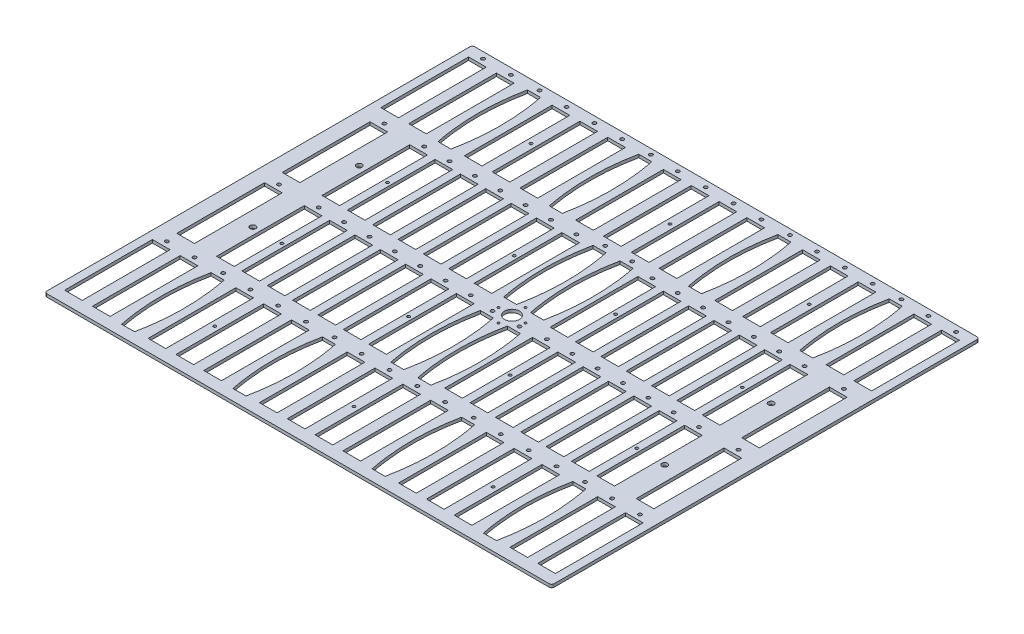
SolidWorks part; units mm, degrees
ref_plane "Front Plane" through (0, 0, 0) normal (0, 0, 1) x (1, 0, 0)
ref_plane "Top Plane" through (0, 0, 0) normal (0, 1, 0) x (1, 0, 0)
ref_plane "Right Plane" through (0, 0, 0) normal (1, 0, 0) x (0, 0, -1)
sketch "Sketch1" plane through (0, 0, 0) normal (0, 1, 0) x (1, 0, 0)
  line L1 (-262.7312, -221.6379) -> (262.7312, -221.6379)
  line L2 (-262.7312, -221.6379) -> (-262.7312, 221.6379)
  line L3 (-262.7312, 221.6379) -> (262.7312, 221.6379)
  line L4 (262.7312, -221.6379) -> (262.7312, 221.6379)
  line L5 (-262.7312, -221.6379) -> (262.7312, 221.6379) construction
  line L6 (-262.7312, 221.6379) -> (262.7312, -221.6379) construction
  point P0 (0, 0)
  dimension "D1" = 525.4625
  dimension "D2" = 443.2757
extrude "Boss-Extrude1" add sketch "Sketch1" along normal blind 3.175
sketch "Sketch2" plane through (0, 3.175, 0) normal (0, 1, 0) x (1, 0, 0)
  circle A0 centre (0, 0) radius 7.62
  dimension "D1" = 15.24
extrude "Cut-Extrude1" cut sketch "Sketch2" against normal through all
hole_wizard "#2 Clearance Hole1" positions "Sketch3" profile "Sketch4" hole size "#2" standard "ANSI Inch" end condition through all
sketch "Sketch3" plane through (0, 3.175, 0) normal (0, 1, 0) x (1, 0, 0)
  line L0 (0, 0) -> (0, 13.97) construction
  line L2 (0, 0) -> (13.97, 0) construction
  line L3 (0, 0) -> (0, -13.97) construction
  line L4 (0, 0) -> (-13.97, 0) construction
  point P194 (0, 13.97)
  point P202 (13.97, 0)
  point P203 (0, -13.97)
  point P204 (-13.97, 0)
  point P205 (0, 0)
  dimension "D1" = 4
  dimension "D2" = 13.97
sketch "Sketch4" plane through (0, 3.175, 0) normal (1, 0, 0) x (0, 0, 1)
  line L0 (0, 0) -> (0, 3.175)
  line L1 (0, 3.175) -> (1.2192, 3.175)
  line L2 (1.2192, 3.175) -> (1.2192, 0)
  line L5 (1.2192, 0) -> (0, 0)
  line L11 (0, -6.35) -> (0, 107.95) construction
  dimension "Thru Hole Dia." = 2.4384
  dimension "Thru Hole Depth" = 3.175
hole_wizard "#1 (0.228) Diameter Hole1" positions "Sketch6" profile "Sketch7" hole size "#1" standard "ANSI Inch" end condition through all
sketch "Sketch6" plane through (0, 3.175, 0) normal (0, 1, 0) x (1, 0, 0)
  line L1 (-213.36, -55.1011) -> (213.36, -55.1011) construction
  line L2 (-213.36, -55.1011) -> (-213.36, 55.1011) construction
  line L3 (-213.36, 55.1011) -> (213.36, 55.1011) construction
  line L4 (213.36, -55.1011) -> (213.36, 55.1011) construction
  line L5 (-213.36, -55.1011) -> (213.36, 55.1011) construction
  line L6 (-213.36, 55.1011) -> (213.36, -55.1011) construction
  circle A0 centre (0, 0) radius 7.62 construction
  point P2 (213.36, 55.1011)
  point P11 (-213.36, -55.1011)
  point P12 (-213.36, 55.1011)
  point P13 (213.36, -55.1011)
  point P26 (-213.36, 55.1011)
  point P28 (213.36, 55.1011)
  point P30 (213.36, -55.1011)
  point P32 (-213.36, -55.1011)
  dimension "D1" = 426.72
  dimension "D2" = 110.2021
  dimension "D3" = 213.36
  dimension "D4" = 55.1011
sketch "Sketch7" plane through (213.36, 3.175, -55.1011) normal (1, 0, 0) x (0, 0, 1)
  line L0 (0, 0) -> (0, 3.175)
  line L1 (0, 3.175) -> (2.8956, 3.175)
  line L2 (2.8956, 3.175) -> (2.8956, 0)
  line L5 (2.8956, 0) -> (0, 0)
  line L11 (0, -6.35) -> (0, 107.95) construction
  dimension "Thru Hole Dia." = 5.7912
  dimension "Thru Hole Depth" = 3.175
sketch "Sketch5" plane through (0, 3.175, 0) normal (0, 1, 0) x (1, 0, 0)
  line L0 (-262.7312, 163.8275) -> (262.7312, 163.8275) construction
  line L1 (-198.8875, 163.8275) -> (-176.0275, 163.8275) construction
  line L2 (-245.1367, 221.6379) -> (-245.1367, -221.6379) construction
  line L3 (-262.7312, 221.6379) -> (-262.7312, -221.6379) construction
  line L4 (-262.7312, -221.6379) -> (262.7312, -221.6379) construction
  line L5 (-216.2971, 221.6379) -> (-216.2971, -221.6379) construction
  line L6 (262.7312, -221.6379) -> (262.7312, 221.6379) construction
  line L7 (-187.4575, 221.6379) -> (-187.4575, -221.6379) construction
  line L8 (-262.7312, 54.6066) -> (262.7312, 54.6066) construction
  line L9 (-262.7312, -54.6142) -> (262.7312, -54.6142) construction
  line L10 (-262.7312, -163.8351) -> (262.7312, -163.8351) construction
  line L11 (262.7312, 221.6379) -> (-262.7312, 221.6379) construction
  line L12 (-158.6179, 221.6379) -> (-158.6179, -221.6379) construction
  line L13 (-129.7783, 221.6379) -> (-129.7783, -221.6379) construction
  line L14 (-100.9388, 221.6379) -> (-100.9388, -221.6379) construction
  line L15 (-72.0992, 221.6379) -> (-72.0992, -221.6379) construction
  line L16 (-43.2596, 221.6379) -> (-43.2596, -221.6379) construction
  line L17 (-14.42, 221.6379) -> (-14.42, -221.6379) construction
  line L18 (14.4196, 221.6379) -> (14.4196, -221.6379) construction
  line L19 (43.2592, 221.6379) -> (43.2592, -221.6379) construction
  line L20 (72.0987, 221.6379) -> (72.0987, -221.6379) construction
  line L21 (100.9383, 221.6379) -> (100.9383, -221.6379) construction
  line L22 (129.7779, 221.6379) -> (129.7779, -221.6379) construction
  line L23 (158.6175, 221.6379) -> (158.6175, -221.6379) construction
  line L24 (187.4571, 221.6379) -> (187.4571, -221.6379) construction
  line L25 (216.2967, 221.6379) -> (216.2967, -221.6379) construction
  line L26 (245.1362, 221.6379) -> (245.1362, -221.6379) construction
  line L27 (-225.4415, 209.2935) -> (-207.1535, 209.2935)
  line L28 (-254.2807, 209.2935) -> (-235.9927, 209.2935)
  line L29 (-254.2807, 209.2935) -> (-254.2807, 118.3615)
  line L30 (-254.2807, 118.3615) -> (-235.9927, 118.3615)
  line L31 (-235.9927, 209.2935) -> (-235.9927, 118.3615)
  line L32 (-254.2807, 209.2935) -> (-235.9927, 118.3615) construction
  line L33 (-254.2807, 118.3615) -> (-235.9927, 209.2935) construction
  line L34 (-254.2807, -118.3691) -> (-235.9927, -118.3691)
  line L35 (-254.2807, -118.3691) -> (-254.2807, -209.3011)
  line L36 (-254.2807, -209.3011) -> (-235.9927, -209.3011)
  line L37 (-235.9927, -118.3691) -> (-235.9927, -209.3011)
  line L38 (-254.2807, -118.3691) -> (-235.9927, -209.3011) construction
  line L39 (-254.2807, -209.3011) -> (-235.9927, -118.3691) construction
  line L40 (-225.4415, 209.2935) -> (-225.4415, 118.3615)
  line L41 (-207.1535, 209.2935) -> (-207.1535, 118.3615)
  line L42 (-225.4415, 118.3615) -> (-207.1535, 118.3615)
  line L43 (-225.4415, -118.3691) -> (-207.1535, -118.3691)
  line L44 (-207.1535, -118.3691) -> (-207.1535, -209.3011)
  line L45 (-225.4415, -118.3691) -> (-225.4415, -209.3011)
  line L46 (-225.4415, -209.3011) -> (-207.1535, -209.3011)
  line L47 (-194.1885, 210.1825) -> (-180.7265, 210.1825)
  line L48 (-194.1885, 210.1825) -> (-194.1885, 117.4725) construction
  line L49 (-194.1885, 117.4725) -> (-180.7265, 117.4725)
  line L50 (-180.7265, 210.1825) -> (-180.7265, 117.4725) construction
  line L51 (-194.1885, 210.1825) -> (-180.7265, 117.4725) construction
  line L52 (-194.1885, 117.4725) -> (-180.7265, 210.1825) construction
  line L53 (-78.8302, 210.1825) -> (-65.3682, 210.1825)
  line L54 (-78.8302, 117.4725) -> (-65.3682, 117.4725)
  line L55 (-167.7632, 209.2935) -> (-149.4752, 209.2935)
  line L56 (-167.7632, 209.2935) -> (-167.7632, 118.3615)
  line L57 (-149.4752, 209.2935) -> (-149.4752, 118.3615)
  line L58 (-167.7632, 118.3615) -> (-149.4752, 118.3615)
  line L59 (-167.7632, -118.3691) -> (-149.4752, -118.3691)
  line L60 (-149.4752, -118.3691) -> (-149.4752, -209.3011)
  line L61 (-167.7632, -118.3691) -> (-167.7632, -209.3011)
  line L62 (-167.7632, -209.3011) -> (-149.4752, -209.3011)
  line L63 (-138.924, 209.2935) -> (-120.636, 209.2935)
  line L64 (-138.924, 209.2935) -> (-138.924, 118.3615)
  line L65 (-120.636, 209.2935) -> (-120.636, 118.3615)
  line L66 (-138.924, 118.3615) -> (-120.636, 118.3615)
  line L67 (-138.924, -118.3691) -> (-120.636, -118.3691)
  line L68 (-120.636, -118.3691) -> (-120.636, -209.3011)
  line L69 (-138.924, -118.3691) -> (-138.924, -209.3011)
  line L70 (-138.924, -209.3011) -> (-120.636, -209.3011)
  line L71 (-110.0849, 209.2935) -> (-91.7969, 209.2935)
  line L72 (-110.0849, 209.2935) -> (-110.0849, 118.3615)
  line L73 (-91.7969, 209.2935) -> (-91.7969, 118.3615)
  line L74 (-110.0849, 118.3615) -> (-91.7969, 118.3615)
  line L75 (-110.0849, -118.3691) -> (-91.7969, -118.3691)
  line L76 (-91.7969, -118.3691) -> (-91.7969, -209.3011)
  line L77 (-110.0849, -118.3691) -> (-110.0849, -209.3011)
  line L78 (-110.0849, -209.3011) -> (-91.7969, -209.3011)
  line L79 (65.3677, 210.1825) -> (78.8297, 210.1825)
  line L80 (65.3677, 117.4725) -> (78.8297, 117.4725)
  line L81 (180.7261, 210.1825) -> (194.1881, 210.1825)
  line L82 (180.7261, 117.4725) -> (194.1881, 117.4725)
  line L83 (-194.1885, -117.6299) -> (-180.7265, -117.6299)
  line L84 (-194.1885, -210.3399) -> (-180.7265, -210.3399)
  line L85 (-78.8302, -117.6299) -> (-65.3682, -117.6299)
  line L86 (-78.8302, -210.3399) -> (-65.3682, -210.3399)
  line L87 (-52.4065, 209.2935) -> (-34.1185, 209.2935)
  line L88 (-52.4065, 209.2935) -> (-52.4065, 118.3615)
  line L89 (-34.1185, 209.2935) -> (-34.1185, 118.3615)
  line L90 (-52.4065, 118.3615) -> (-34.1185, 118.3615)
  line L91 (-52.4065, -118.3691) -> (-34.1185, -118.3691)
  line L92 (-34.1185, -118.3691) -> (-34.1185, -209.3011)
  line L93 (-52.4065, -118.3691) -> (-52.4065, -209.3011)
  line L94 (-52.4065, -209.3011) -> (-34.1185, -209.3011)
  line L95 (-23.5674, 209.2935) -> (-5.2794, 209.2935)
  line L96 (-23.5674, 209.2935) -> (-23.5674, 118.3615)
  line L97 (-5.2794, 209.2935) -> (-5.2794, 118.3615)
  line L98 (-23.5674, 118.3615) -> (-5.2794, 118.3615)
  line L99 (-23.5674, -118.3691) -> (-5.2794, -118.3691)
  line L100 (-5.2794, -118.3691) -> (-5.2794, -209.3011)
  line L101 (-23.5674, -118.3691) -> (-23.5674, -209.3011)
  line L102 (-23.5674, -209.3011) -> (-5.2794, -209.3011)
  line L103 (5.2718, 209.2935) -> (23.5598, 209.2935)
  line L104 (5.2718, 209.2935) -> (5.2718, 118.3615)
  line L105 (23.5598, 209.2935) -> (23.5598, 118.3615)
  line L106 (5.2718, 118.3615) -> (23.5598, 118.3615)
  line L107 (5.2718, -118.3691) -> (23.5598, -118.3691)
  line L108 (23.5598, -118.3691) -> (23.5598, -209.3011)
  line L109 (5.2718, -118.3691) -> (5.2718, -209.3011)
  line L110 (5.2718, -209.3011) -> (23.5598, -209.3011)
  line L111 (34.1109, 209.2935) -> (52.3989, 209.2935)
  line L112 (34.1109, 209.2935) -> (34.1109, 118.3615)
  line L113 (52.3989, 209.2935) -> (52.3989, 118.3615)
  line L114 (34.1109, 118.3615) -> (52.3989, 118.3615)
  line L115 (34.1109, -118.3691) -> (52.3989, -118.3691)
  line L116 (52.3989, -118.3691) -> (52.3989, -209.3011)
  line L117 (34.1109, -118.3691) -> (34.1109, -209.3011)
  line L118 (34.1109, -209.3011) -> (52.3989, -209.3011)
  line L119 (180.7261, -117.6299) -> (194.1881, -117.6299)
  line L120 (180.7261, -210.3399) -> (194.1881, -210.3399)
  line L121 (65.3677, -210.3399) -> (78.8297, -210.3399)
  line L122 (65.3677, -117.6299) -> (78.8297, -117.6299)
  line L127 (91.7892, 209.2935) -> (110.0772, 209.2935)
  line L128 (91.7892, 209.2935) -> (91.7893, 118.3615)
  line L129 (110.0772, 209.2935) -> (110.0773, 118.3615)
  line L130 (91.7893, 118.3615) -> (110.0773, 118.3615)
  line L131 (91.7893, -118.3691) -> (110.0773, -118.3691)
  line L132 (110.0773, -118.3691) -> (110.0773, -209.3011)
  line L133 (91.7893, -118.3691) -> (91.7893, -209.3011)
  line L134 (91.7893, -209.3011) -> (110.0773, -209.3011)
  line L135 (120.6284, 209.2935) -> (138.9164, 209.2935)
  line L136 (120.6284, 209.2935) -> (120.6284, 118.3615)
  line L137 (138.9164, 209.2935) -> (138.9164, 118.3615)
  line L138 (120.6284, 118.3615) -> (138.9164, 118.3615)
  line L139 (120.6284, -118.3691) -> (138.9164, -118.3691)
  line L140 (138.9164, -118.3691) -> (138.9164, -209.3011)
  line L141 (120.6284, -118.3691) -> (120.6284, -209.3011)
  line L142 (120.6284, -209.3011) -> (138.9164, -209.3011)
  line L143 (149.4676, 209.2935) -> (167.7556, 209.2935)
  line L144 (149.4676, 209.2935) -> (149.4676, 118.3615)
  line L145 (167.7556, 209.2935) -> (167.7556, 118.3615)
  line L146 (149.4676, 118.3615) -> (167.7556, 118.3615)
  line L147 (149.4676, -118.3691) -> (167.7556, -118.3691)
  line L148 (167.7556, -118.3691) -> (167.7556, -209.3011)
  line L149 (149.4676, -118.3691) -> (149.4676, -209.3011)
  line L150 (149.4676, -209.3011) -> (167.7556, -209.3011)
  line L159 (207.1459, 209.2935) -> (225.4339, 209.2935)
  line L160 (207.1459, 209.2935) -> (207.1459, 118.3615)
  line L161 (225.4339, 209.2935) -> (225.4339, 118.3615)
  line L162 (207.1459, 118.3615) -> (225.4339, 118.3615)
  line L163 (207.1459, -118.3691) -> (225.4339, -118.3691)
  line L164 (225.4339, -118.3691) -> (225.4339, -209.3011)
  line L165 (207.1459, -118.3691) -> (207.1459, -209.3011)
  line L166 (207.1459, -209.3011) -> (225.4339, -209.3011)
  line L167 (235.985, 209.2935) -> (254.2731, 209.2935)
  line L168 (235.985, 209.2935) -> (235.9851, 118.3615)
  line L169 (254.2731, 209.2935) -> (254.2731, 118.3615)
  line L170 (235.9851, 118.3615) -> (254.2731, 118.3615)
  line L171 (235.9851, -118.3691) -> (254.2731, -118.3691)
  line L172 (254.2731, -118.3691) -> (254.2731, -209.3011)
  line L173 (235.9851, -118.3691) -> (235.9851, -209.3011)
  line L174 (235.9851, -209.3011) -> (254.2731, -209.3011)
  line L337 (-178.3143, 209.2935) -> (-178.3143, 118.3615) [skipped]
  line L338 (-196.6023, 118.3615) -> (-178.3143, 118.3615) [skipped]
  line L339 (-196.6023, 209.2935) -> (-196.6023, 118.3615) [skipped]
  line L340 (-196.6023, 209.2935) -> (-178.3143, 209.2935) [skipped]
  line L341 (-62.9577, 209.2935) -> (-62.9577, 118.3615) [skipped]
  line L342 (-81.2457, 209.2935) -> (-62.9577, 209.2935) [skipped]
  line L343 (-81.2457, 209.2935) -> (-81.2457, 118.3615) [skipped]
  line L344 (-81.2457, 118.3615) -> (-62.9577, 118.3615) [skipped]
  line L345 (-196.6023, -118.3691) -> (-178.3143, -118.3691) [skipped]
  line L346 (-196.6023, -209.3011) -> (-178.3143, -209.3011) [skipped]
  line L347 (-178.3143, -118.3691) -> (-178.3143, -209.3011) [skipped]
  line L348 (-196.6023, -118.3691) -> (-196.6023, -209.3011) [skipped]
  line L349 (-81.2457, -118.3691) -> (-62.9577, -118.3691) [skipped]
  line L350 (-81.2457, -118.3691) -> (-81.2457, -209.3011) [skipped]
  line L351 (-62.9577, -118.3691) -> (-62.9577, -209.3011) [skipped]
  line L352 (-81.2457, -209.3011) -> (-62.9577, -209.3011) [skipped]
  line L353 (178.3067, -118.3691) -> (196.5947, -118.3691) [skipped]
  line L354 (196.5947, -118.3691) -> (196.5947, -209.3011) [skipped]
  line L355 (178.3067, -118.3691) -> (178.3067, -209.3011) [skipped]
  line L356 (178.3067, -209.3011) -> (196.5947, -209.3011) [skipped]
  line L357 (62.9501, -209.3011) -> (81.2381, -209.3011) [skipped]
  line L358 (81.2381, -118.3691) -> (81.2381, -209.3011) [skipped]
  line L359 (62.9501, -118.3691) -> (62.9501, -209.3011) [skipped]
  line L360 (62.9501, -118.3691) -> (81.2381, -118.3691) [skipped]
  line L361 (178.3067, 118.3615) -> (196.5947, 118.3615) [skipped]
  line L362 (196.5947, 209.2935) -> (196.5947, 118.3615) [skipped]
  line L363 (178.3067, 209.2935) -> (178.3067, 118.3615) [skipped]
  line L364 (178.3067, 209.2935) -> (196.5947, 209.2935) [skipped]
  line L365 (62.9501, 118.3615) -> (81.2381, 118.3615) [skipped]
  line L366 (62.9501, 209.2935) -> (62.9501, 118.3615) [skipped]
  line L367 (81.2381, 209.2935) -> (81.2381, 118.3615) [skipped]
  line L368 (62.9501, 209.2935) -> (81.2381, 209.2935) [skipped]
  circle A0 centre (-245.1367, 215.1355) radius 1.8288
  circle A1 centre (-245.1367, -112.5271) radius 1.8288
  circle A2 centre (-216.2975, 215.1355) radius 1.8288
  circle A3 centre (-216.2975, -112.5271) radius 1.8288
  circle A4 centre (-187.4575, 216.0245) radius 1.8288
  circle A5 centre (-72.0992, 216.0245) radius 1.8288
  circle A6 centre (-158.6192, 215.1355) radius 1.8288
  circle A7 centre (-158.6192, -112.5271) radius 1.8288
  circle A8 centre (-129.78, 215.1355) radius 1.8288
  circle A9 centre (-129.78, -112.5271) radius 1.8288
  circle A10 centre (-100.9409, 215.1355) radius 1.8288
  circle A11 centre (-100.9409, -112.5271) radius 1.8288
  circle A12 centre (72.0987, 216.0245) radius 1.8288
  circle A13 centre (187.4571, 216.0245) radius 1.8288
  circle A14 centre (-43.2625, 215.1355) radius 1.8288
  circle A15 centre (-43.2625, -112.5271) radius 1.8288
  circle A16 centre (-14.4234, 215.1355) radius 1.8288
  circle A17 centre (-14.4234, -112.5271) radius 1.8288
  circle A18 centre (14.4158, 215.1355) radius 1.8288
  circle A19 centre (14.4158, -112.5271) radius 1.8288
  circle A20 centre (43.2549, 215.1355) radius 1.8288
  circle A21 centre (43.2549, -112.5271) radius 1.8288
  circle A22 centre (-187.4575, -111.7879) radius 1.8288
  circle A23 centre (-72.0992, -111.7879) radius 1.8288
  circle A24 centre (100.9333, 215.1355) radius 1.8288
  circle A25 centre (100.9333, -112.5271) radius 1.8288
  circle A26 centre (129.7724, 215.1355) radius 1.8288
  circle A27 centre (129.7724, -112.5271) radius 1.8288
  circle A28 centre (158.6116, 215.1355) radius 1.8288
  circle A29 centre (158.6116, -112.5271) radius 1.8288
  circle A30 centre (187.4571, -111.7879) radius 1.8288
  circle A31 centre (72.0987, -111.7879) radius 1.8288
  circle A32 centre (216.2899, 215.1355) radius 1.8288
  circle A33 centre (216.2899, -112.5271) radius 1.8288
  circle A34 centre (245.129, 215.1355) radius 1.8288
  circle A35 centre (245.1291, -112.5271) radius 1.8288
  circle A36 centre (-72.1017, 215.1355) radius 1.8288 [skipped]
  circle A37 centre (-187.4583, 215.1355) radius 1.8288 [skipped]
  circle A38 centre (-187.4583, -112.5271) radius 1.8288 [skipped]
  circle A39 centre (-72.1017, -112.5271) radius 1.8288 [skipped]
  circle A40 centre (187.4507, -112.5271) radius 1.8288 [skipped]
  circle A41 centre (72.0941, -112.5271) radius 1.8288 [skipped]
  circle A42 centre (187.4507, 215.1355) radius 1.8288 [skipped]
  circle A43 centre (72.0941, 215.1355) radius 1.8288 [skipped]
  spline S0 degree 2 poles (-180.7265, 210.1825) (-171.3285, 163.8275) (-180.7265, 117.4725) knots 0 0 0 1 1 1
  spline S1 degree 2 poles (-194.1885, 210.1825) (-203.5865, 163.8275) (-194.1885, 117.4725) knots 0 0 0 1 1 1
  spline S2 degree 2 poles (-78.8302, 210.1825) (-88.2282, 163.8275) (-78.8302, 117.4725) knots 0 0 0 1 1 1
  spline S3 degree 2 poles (-65.3682, 210.1825) (-55.9702, 163.8275) (-65.3682, 117.4725) knots 0 0 0 1 1 1
  spline S4 degree 2 poles (65.3677, 210.1825) (55.9697, 163.8275) (65.3677, 117.4725) knots 0 0 0 1 1 1
  spline S5 degree 2 poles (78.8297, 210.1825) (88.2277, 163.8275) (78.8297, 117.4725) knots 0 0 0 1 1 1
  spline S6 degree 2 poles (194.1881, 210.1825) (203.5861, 163.8275) (194.1881, 117.4725) knots 0 0 0 1 1 1
  spline S7 degree 2 poles (180.7261, 210.1825) (171.3281, 163.8275) (180.7261, 117.4725) knots 0 0 0 1 1 1
  spline S8 degree 2 poles (-194.1885, -117.6299) (-203.5865, -163.9849) (-194.1885, -210.3399) knots 0 0 0 1 1 1
  spline S9 degree 2 poles (-180.7265, -117.6299) (-171.3285, -163.9849) (-180.7265, -210.3399) knots 0 0 0 1 1 1
  spline S10 degree 2 poles (-65.3682, -117.6299) (-55.9702, -163.9849) (-65.3682, -210.3399) knots 0 0 0 1 1 1
  spline S11 degree 2 poles (-78.8302, -117.6299) (-88.2282, -163.9849) (-78.8302, -210.3399) knots 0 0 0 1 1 1
  spline S12 degree 2 poles (194.1881, -117.6299) (203.5861, -163.9849) (194.1881, -210.3399) knots 0 0 0 1 1 1
  spline S13 degree 2 poles (180.7261, -117.6299) (171.3281, -163.9849) (180.7261, -210.3399) knots 0 0 0 1 1 1
  spline S14 degree 2 poles (78.8297, -117.6299) (88.2277, -163.9849) (78.8297, -210.3399) knots 0 0 0 1 1 1
  spline S15 degree 2 poles (65.3677, -117.6299) (55.9697, -163.9849) (65.3677, -210.3399) knots 0 0 0 1 1 1
  point P18 (-245.1367, 163.8275)
  point P57 (-245.1367, -163.8351)
  point P66 (-187.4575, 163.8275)
  point P86 (-187.4575, 163.8275)
  dimension "D6" = 3.6576
  dimension "D7" = 5.842
  dimension "D8" = 5.842
  dimension "D13" = 5.842
  dimension "D1" = 4
  dimension "D3" = 17.5946
  dimension "D5" = 90.932
  dimension "D2" = 57.8104
  dimension "D4" = 18.288
  dimension "D10" = 13.462
  dimension "D11" = 92.71
  dimension "D12" = 22.86
  dimension "D9" = 18
  dimension "D14" = 2
  dimension "D15" = 2
extrude "Cut-Extrude3" cut sketch "Sketch5" against normal blind 3.175
hole_wizard "#6 Clearance Hole2" positions "Sketch9" profile "Sketch10" hole size "#6" standard "ANSI Inch" end condition through all
sketch "Sketch9" plane through (0, 3.175, 0) normal (0, 1, 0) x (1, 0, 0)
  line L0 (-245.1367, 209.2935) -> (-245.1367, 215.1355) construction
  line L1 (-235.9927, 209.2935) -> (-254.2807, 209.2935) construction
  point P2 (-245.1367, 215.1355)
  dimension "D1" = 5.842
sketch "Sketch10" plane through (-245.1367, 3.175, -215.1355) normal (1, 0, 0) x (0, 0, 1)
  line L0 (0, 0) -> (0, 3.175)
  line L1 (0, 3.175) -> (1.8288, 3.175)
  line L2 (1.8288, 3.175) -> (1.8288, 0)
  line L5 (1.8288, 0) -> (0, 0)
  line L11 (0, -6.35) -> (0, 107.95) construction
  dimension "Thru Hole Dia." = 3.6576
  dimension "Thru Hole Depth" = 3.175
sketch "Sketch11" plane through (0, 3.175, 0) normal (0, 1, 0) x (1, 0, 0)
  line L0 (-262.7312, 163.8275) -> (262.7312, 163.8275) construction
  line L1 (-262.7312, 221.6379) -> (-262.7312, -221.6379) construction
  line L2 (262.7312, -221.6379) -> (262.7312, 221.6379) construction
  line L3 (262.7312, 221.6379) -> (-262.7312, 221.6379) construction
  line L4 (-262.7312, 54.5567) -> (262.7312, 54.5567) construction
  line L5 (-262.7312, -54.7141) -> (262.7312, -54.7141) construction
  line L6 (-262.7312, -163.9849) -> (262.7312, -163.9849) construction
  line L7 (-238.045, 100.0227) -> (-238.045, 105.8647) construction
  line L8 (-247.189, 100.0227) -> (-228.901, 100.0227)
  line L9 (-247.189, 100.0227) -> (-247.189, 9.0907)
  line L10 (-247.189, 9.0907) -> (-228.901, 9.0907)
  line L11 (-228.901, 100.0227) -> (-228.901, 9.0907)
  line L12 (-247.189, 100.0227) -> (-228.901, 9.0907) construction
  line L13 (-247.189, 9.0907) -> (-228.901, 100.0227) construction
  line L14 (228.901, 100.0227) -> (247.189, 100.0227)
  line L15 (228.901, 100.0227) -> (228.901, 9.0907)
  line L16 (247.189, 100.0227) -> (247.189, 9.0907)
  line L17 (228.901, 9.0907) -> (247.189, 9.0907)
  line L18 (228.901, -9.2481) -> (247.189, -9.2481)
  line L19 (228.901, -9.2481) -> (228.901, -100.1801)
  line L20 (247.189, -9.2481) -> (247.189, -100.1801)
  line L21 (228.901, -100.1801) -> (247.189, -100.1801)
  line L22 (-247.189, -9.2481) -> (-228.901, -9.2481)
  line L23 (-247.189, -9.2481) -> (-247.189, -100.1801)
  line L24 (-228.901, -9.2481) -> (-228.901, -100.1801)
  line L25 (-247.189, -100.1801) -> (-228.901, -100.1801)
  circle A0 centre (-238.045, 105.8647) radius 1.8288
  circle A1 centre (238.045, 105.8647) radius 1.8288
  circle A2 centre (238.045, -3.4061) radius 1.8288
  circle A3 centre (-238.045, -3.4061) radius 1.8288
  point P8 (-238.045, 54.5567)
  dimension "D5" = 3.6576
  dimension "D1" = 57.8104
  dimension "D2" = 24.6863
  dimension "D3" = 18.288
  dimension "D4" = 90.932
  dimension "D6" = 5.842
extrude "Cut-Extrude5" cut sketch "Sketch11" against normal blind 3.175
sketch "Sketch12" plane through (0, 3.175, 0) normal (0, 1, 0) x (1, 0, 0)
  line L0 (-228.901, 54.5567) -> (228.901, 54.5567) construction
  line L1 (-228.901, 9.0907) -> (-228.901, 100.0227) construction
  line L2 (228.901, 100.0227) -> (228.901, 9.0907) construction
  line L3 (-213.36, 55.1011) -> (-213.36, 247.1712) construction
  line L4 (-247.189, 9.0907) -> (-228.901, 9.0907) construction
  line L5 (-205.994, 100.0227) -> (-187.706, 100.0227)
  line L6 (-205.994, 100.0227) -> (-205.994, 9.0907)
  line L7 (-205.994, 9.0907) -> (-187.706, 9.0907)
  line L8 (-187.706, 100.0227) -> (-187.706, 9.0907)
  line L9 (-205.994, 100.0227) -> (-187.706, 9.0907) construction
  line L10 (-205.994, 9.0907) -> (-187.706, 100.0227) construction
  line L11 (-196.85, 100.0227) -> (-196.85, 105.8647) construction
  line L12 (-179.7209, 100.0227) -> (-161.4329, 100.0227)
  line L13 (-179.7209, 100.0227) -> (-179.7209, 9.0907)
  line L14 (-161.4329, 100.0227) -> (-161.4329, 9.0907)
  line L15 (-179.7209, 9.0907) -> (-161.4329, 9.0907)
  line L16 (-153.4477, 100.0227) -> (-135.1597, 100.0227)
  line L17 (-153.4477, 100.0227) -> (-153.4477, 9.0907)
  line L18 (-135.1597, 100.0227) -> (-135.1597, 9.0907)
  line L19 (-153.4477, 9.0907) -> (-135.1597, 9.0907)
  line L20 (-127.1746, 100.0227) -> (-108.8866, 100.0227)
  line L21 (-127.1746, 100.0227) -> (-127.1746, 9.0907)
  line L22 (-108.8866, 100.0227) -> (-108.8866, 9.0907)
  line L23 (-127.1746, 9.0907) -> (-108.8866, 9.0907)
  line L24 (-100.9015, 100.0227) -> (-82.6135, 100.0227)
  line L25 (-100.9015, 100.0227) -> (-100.9015, 9.0907)
  line L26 (-82.6135, 100.0227) -> (-82.6135, 9.0907)
  line L27 (-100.9015, 9.0907) -> (-82.6135, 9.0907)
  line L28 (-74.6284, 100.0227) -> (-56.3404, 100.0227)
  line L29 (-74.6284, 100.0227) -> (-74.6284, 9.0907)
  line L30 (-56.3404, 100.0227) -> (-56.3404, 9.0907)
  line L31 (-74.6284, 9.0907) -> (-56.3404, 9.0907)
  line L32 (-48.3552, 100.0227) -> (-30.0672, 100.0227)
  line L33 (-48.3552, 100.0227) -> (-48.3552, 9.0907)
  line L34 (-30.0672, 100.0227) -> (-30.0672, 9.0907)
  line L35 (-48.3552, 9.0907) -> (-30.0672, 9.0907)
  line L36 (0, 0) -> (0, 123.4666) construction
  line L37 (-13.97, 58.3667) -> (13.97, 58.3667) construction
  line L38 (-2.54, 58.3667) -> (-25.4, 58.3667) construction
  line L39 (-7.239, 104.7217) -> (-20.701, 104.7217)
  line L40 (-7.239, 104.7217) -> (-7.239, 12.0117) construction
  line L41 (-7.239, 12.0117) -> (-20.701, 12.0117)
  line L42 (-20.701, 104.7217) -> (-20.701, 12.0117) construction
  line L43 (-7.239, 104.7217) -> (-20.701, 12.0117) construction
  line L44 (30.4641, 100.0227) -> (48.7521, 100.0227)
  line L45 (30.4641, 100.0227) -> (30.4641, 9.0907)
  line L46 (48.7521, 100.0227) -> (48.7521, 9.0907)
  line L47 (30.4641, 9.0907) -> (48.7521, 9.0907)
  line L48 (56.7373, 100.0227) -> (75.0253, 100.0227)
  line L49 (56.7373, 100.0227) -> (56.7373, 9.0907)
  line L50 (75.0253, 100.0227) -> (75.0253, 9.0907)
  line L51 (56.7373, 9.0907) -> (75.0253, 9.0907)
  line L52 (83.0104, 100.0227) -> (101.2984, 100.0227)
  line L53 (83.0104, 100.0227) -> (83.0104, 9.0907)
  line L54 (101.2984, 100.0227) -> (101.2984, 9.0907)
  line L55 (83.0104, 9.0907) -> (101.2984, 9.0907)
  line L56 (109.2835, 100.0227) -> (127.5715, 100.0227)
  line L57 (109.2835, 100.0227) -> (109.2835, 9.0907)
  line L58 (127.5715, 100.0227) -> (127.5715, 9.0907)
  line L59 (109.2835, 9.0907) -> (127.5715, 9.0907)
  line L60 (135.5566, 100.0227) -> (153.8446, 100.0227)
  line L61 (135.5566, 100.0227) -> (135.5566, 9.0907)
  line L62 (153.8446, 100.0227) -> (153.8446, 9.0907)
  line L63 (135.5566, 9.0907) -> (153.8446, 9.0907)
  line L64 (161.8298, 100.0227) -> (180.1178, 100.0227)
  line L65 (161.8298, 100.0227) -> (161.8298, 9.0907)
  line L66 (180.1178, 100.0227) -> (180.1178, 9.0907)
  line L67 (161.8298, 9.0907) -> (180.1178, 9.0907)
  line L68 (188.1029, 100.0227) -> (206.3909, 100.0227)
  line L69 (188.1029, 100.0227) -> (188.1029, 9.0907)
  line L70 (206.3909, 100.0227) -> (206.3909, 9.0907)
  line L71 (188.1029, 9.0907) -> (206.3909, 9.0907)
  line L72 (-179.7209, -9.2481) -> (-161.4329, -9.2481)
  line L73 (-179.7209, -9.2481) -> (-179.7209, -100.1801)
  line L74 (-161.4329, -9.2481) -> (-161.4329, -100.1801)
  line L75 (-179.7209, -100.1801) -> (-161.4329, -100.1801)
  line L76 (-153.4477, -9.2481) -> (-135.1597, -9.2481)
  line L77 (-153.4477, -9.2481) -> (-153.4477, -100.1801)
  line L78 (-135.1597, -9.2481) -> (-135.1597, -100.1801)
  line L79 (-153.4477, -100.1801) -> (-135.1597, -100.1801)
  line L80 (-127.1746, -9.2481) -> (-108.8866, -9.2481)
  line L81 (-127.1746, -9.2481) -> (-127.1746, -100.1801)
  line L82 (-108.8866, -9.2481) -> (-108.8866, -100.1801)
  line L83 (-127.1746, -100.1801) -> (-108.8866, -100.1801)
  line L84 (-100.9015, -9.2481) -> (-82.6135, -9.2481)
  line L85 (-100.9015, -9.2481) -> (-100.9015, -100.1801)
  line L86 (-82.6135, -9.2481) -> (-82.6135, -100.1801)
  line L87 (-100.9015, -100.1801) -> (-82.6135, -100.1801)
  line L88 (-74.6284, -9.2481) -> (-56.3404, -9.2481)
  line L89 (-74.6284, -9.2481) -> (-74.6284, -100.1801)
  line L90 (-56.3404, -9.2481) -> (-56.3404, -100.1801)
  line L91 (-74.6284, -100.1801) -> (-56.3404, -100.1801)
  line L92 (-48.3552, -9.2481) -> (-30.0672, -9.2481)
  line L93 (-48.3552, -9.2481) -> (-48.3552, -100.1801)
  line L94 (-30.0672, -9.2481) -> (-30.0672, -100.1801)
  line L95 (-48.3552, -100.1801) -> (-30.0672, -100.1801)
  line L96 (-7.239, 12.0117) -> (-20.701, 104.7217) construction
  line L97 (-13.97, 104.7217) -> (-13.97, 110.5637) construction
  line L98 (2.54, 58.3667) -> (25.4, 58.3667) construction
  line L99 (7.239, 12.0117) -> (20.701, 12.0117)
  line L100 (7.239, 12.0117) -> (7.239, 104.7217) construction
  line L101 (7.239, 104.7217) -> (20.701, 104.7217)
  line L102 (20.701, 12.0117) -> (20.701, 104.7217) construction
  line L103 (7.239, 12.0117) -> (20.701, 104.7217) construction
  line L104 (30.4641, -9.2481) -> (48.7521, -9.2481)
  line L105 (30.4641, -9.2481) -> (30.4641, -100.1801)
  line L106 (48.7521, -9.2481) -> (48.7521, -100.1801)
  line L107 (30.4641, -100.1801) -> (48.7521, -100.1801)
  line L108 (56.7373, -9.2481) -> (75.0253, -9.2481)
  line L109 (56.7373, -9.2481) -> (56.7373, -100.1801)
  line L110 (75.0253, -9.2481) -> (75.0253, -100.1801)
  line L111 (56.7373, -100.1801) -> (75.0253, -100.1801)
  line L112 (83.0104, -9.2481) -> (101.2984, -9.2481)
  line L113 (83.0104, -9.2481) -> (83.0104, -100.1801)
  line L114 (101.2984, -9.2481) -> (101.2984, -100.1801)
  line L115 (83.0104, -100.1801) -> (101.2984, -100.1801)
  line L116 (109.2835, -9.2481) -> (127.5715, -9.2481)
  line L117 (109.2835, -9.2481) -> (109.2835, -100.1801)
  line L118 (127.5715, -9.2481) -> (127.5715, -100.1801)
  line L119 (109.2835, -100.1801) -> (127.5715, -100.1801)
  line L120 (135.5566, -9.2481) -> (153.8446, -9.2481)
  line L121 (135.5566, -9.2481) -> (135.5566, -100.1801)
  line L122 (153.8446, -9.2481) -> (153.8446, -100.1801)
  line L123 (135.5566, -100.1801) -> (153.8446, -100.1801)
  line L124 (161.8298, -9.2481) -> (180.1178, -9.2481)
  line L125 (161.8298, -9.2481) -> (161.8298, -100.1801)
  line L126 (180.1178, -9.2481) -> (180.1178, -100.1801)
  line L127 (161.8298, -100.1801) -> (180.1178, -100.1801)
  line L128 (188.1029, -9.2481) -> (206.3909, -9.2481)
  line L129 (188.1029, -9.2481) -> (188.1029, -100.1801)
  line L130 (206.3909, -9.2481) -> (206.3909, -100.1801)
  line L131 (188.1029, -100.1801) -> (206.3909, -100.1801)
  line L132 (-205.994, -9.2481) -> (-187.706, -9.2481)
  line L133 (-205.994, -9.2481) -> (-205.994, -100.1801)
  line L134 (-187.706, -9.2481) -> (-187.706, -100.1801)
  line L135 (-205.994, -100.1801) -> (-187.706, -100.1801)
  line L136 (-22.0821, 100.0227) -> (-3.7941, 100.0227) [skipped]
  line L137 (-22.0821, 100.0227) -> (-22.0821, 9.0907) [skipped]
  line L138 (-3.7941, 100.0227) -> (-3.7941, 9.0907) [skipped]
  line L139 (-22.0821, 9.0907) -> (-3.7941, 9.0907) [skipped]
  line L140 (4.191, 100.0227) -> (22.479, 100.0227) [skipped]
  line L141 (4.191, 100.0227) -> (4.191, 9.0907) [skipped]
  line L142 (22.479, 100.0227) -> (22.479, 9.0907) [skipped]
  line L143 (4.191, 9.0907) -> (22.479, 9.0907) [skipped]
  line L144 (-22.0821, -9.2481) -> (-3.7941, -9.2481) [skipped]
  line L145 (-22.0821, -9.2481) -> (-22.0821, -100.1801) [skipped]
  line L146 (-3.7941, -9.2481) -> (-3.7941, -100.1801) [skipped]
  line L147 (-22.0821, -100.1801) -> (-3.7941, -100.1801) [skipped]
  line L148 (4.191, -9.2481) -> (22.479, -9.2481) [skipped]
  line L149 (4.191, -9.2481) -> (4.191, -100.1801) [skipped]
  line L150 (22.479, -9.2481) -> (22.479, -100.1801) [skipped]
  line L151 (4.191, -100.1801) -> (22.479, -100.1801) [skipped]
  line L152 (7.239, 104.7217) -> (20.701, 12.0117) construction
  line L154 (13.97, 104.7217) -> (13.97, 110.5637) construction
  line L155 (-7.239, -12.1183) -> (-20.701, -12.1183)
  line L156 (7.239, -12.1183) -> (20.701, -12.1183)
  line L157 (7.239, -104.8283) -> (20.701, -104.8283)
  line L158 (-7.239, -104.8283) -> (-20.701, -104.8283)
  circle A0 centre (-196.85, 105.8647) radius 1.8288
  circle A1 centre (-238.045, 105.8647) radius 1.8288 construction
  circle A2 centre (-170.5769, 105.8647) radius 1.8288
  circle A3 centre (-144.3037, 105.8647) radius 1.8288
  circle A4 centre (-118.0306, 105.8647) radius 1.8288
  circle A5 centre (-91.7575, 105.8647) radius 1.8288
  circle A6 centre (-65.4844, 105.8647) radius 1.8288
  circle A7 centre (-39.2112, 105.8647) radius 1.8288
  circle A8 centre (-13.97, 110.5637) radius 1.8288
  circle A9 centre (13.97, 110.5637) radius 1.8288
  circle A10 centre (39.6081, 105.8647) radius 1.8288
  circle A11 centre (65.8813, 105.8647) radius 1.8288
  circle A12 centre (92.1544, 105.8647) radius 1.8288
  circle A13 centre (118.4275, 105.8647) radius 1.8288
  circle A14 centre (144.7006, 105.8647) radius 1.8288
  circle A15 centre (170.9738, 105.8647) radius 1.8288
  circle A16 centre (197.2469, 105.8647) radius 1.8288
  circle A17 centre (-170.5769, -3.4061) radius 1.8288
  circle A18 centre (-144.3037, -3.4061) radius 1.8288
  circle A19 centre (-118.0306, -3.4061) radius 1.8288
  circle A20 centre (-91.7575, -3.4061) radius 1.8288
  circle A21 centre (-65.4844, -3.4061) radius 1.8288
  circle A22 centre (-39.2112, -3.4061) radius 1.8288
  circle A23 centre (13.97, -6.2763) radius 1.8288
  circle A24 centre (-13.97, -6.2763) radius 1.8288
  circle A25 centre (39.6081, -3.4061) radius 1.8288
  circle A26 centre (65.8813, -3.4061) radius 1.8288
  circle A27 centre (92.1544, -3.4061) radius 1.8288
  circle A28 centre (118.4275, -3.4061) radius 1.8288
  circle A29 centre (144.7006, -3.4061) radius 1.8288
  circle A30 centre (170.9738, -3.4061) radius 1.8288
  circle A31 centre (197.2469, -3.4061) radius 1.8288
  circle A32 centre (-196.85, -3.4061) radius 1.8288
  circle A33 centre (-12.9381, 105.8647) radius 1.8288 [skipped]
  circle A34 centre (13.335, 105.8647) radius 1.8288 [skipped]
  circle A35 centre (-12.9381, -3.4061) radius 1.8288 [skipped]
  circle A36 centre (13.335, -3.4061) radius 1.8288 [skipped]
  spline S0 degree 2 poles (-20.701, 104.7217) (-30.099, 58.3667) (-20.701, 12.0117) knots 0 0 0 1 1 1
  spline S1 degree 2 poles (-7.239, 104.7217) (2.159, 58.3667) (-7.239, 12.0117) knots 0 0 0 1 1 1
  spline S2 degree 2 poles (20.701, 104.7217) (30.099, 58.3667) (20.701, 12.0117) knots 0 0 0 1 1 1
  spline S3 degree 2 poles (7.239, 104.7217) (-2.159, 58.3667) (7.239, 12.0117) knots 0 0 0 1 1 1
  spline S4 degree 2 poles (-7.239, -12.1183) (2.159, -58.4733) (-7.239, -104.8283) knots 0 0 0 1 1 1
  spline S5 degree 2 poles (-20.701, -12.1183) (-30.099, -58.4733) (-20.701, -104.8283) knots 0 0 0 1 1 1
  spline S6 degree 2 poles (7.239, -12.1183) (-2.159, -58.4733) (7.239, -104.8283) knots 0 0 0 1 1 1
  spline S7 degree 2 poles (20.701, -12.1183) (30.099, -58.4733) (20.701, -104.8283) knots 0 0 0 1 1 1
  point P9 (-196.85, 54.5567)
  point P61 (0, 58.3667)
  point P69 (-13.97, 58.3667)
  point P159 (13.97, 58.3667)
  dimension "D1" = 5.842
  dimension "D8" = 92.71
  dimension "D2" = 16.51
  dimension "D5" = 3.81
  dimension "D6" = 27.94
  dimension "D7" = 13.462
  dimension "D9" = 22.86
  dimension "D10" = 5.842
  dimension "D11" = 30.0672
  dimension "D3" = 16
  dimension "D4" = 2
  dimension "D13" = 2
  dimension "D14" = 2
extrude "Cut-Extrude6" cut sketch "Sketch12" against normal blind 3.175
fillet "Fillet1" radius 2.54 4 edges at (-262.7312, 1.5875, -221.6379) (-262.7312, 1.5875, 221.6379) (262.7312, 1.5875, 221.6379) (262.7312, 1.5875, -221.6379)
hole_wizard "#4 Clearance Hole1" positions "Sketch13" profile "Sketch14" hole size "#4" standard "ANSI Inch" end condition through all
sketch "Sketch13" plane through (0, 3.175, 0) normal (0, 1, 0) x (1, 0, 0)
  line L0 (-254.2807, 163.8275) -> (254.2731, 163.8275) construction
  line L1 (-254.2807, 209.2935) -> (-254.2807, 118.3615) construction
  line L2 (254.2731, 118.3615) -> (254.2731, 209.2935) construction
  line L4 (-149.4752, 209.2935) -> (-138.924, 118.3615) construction
  line L6 (-5.2794, 209.2935) -> (5.2718, 118.3615) construction
  line L7 (138.9164, 209.2935) -> (149.4676, 118.3615) construction
  line L8 (-187.706, 100.0227) -> (-179.7209, 9.0907) construction
  line L9 (-56.3404, 100.0227) -> (-48.3552, 9.0907) construction
  line L10 (48.7521, 100.0227) -> (56.7373, 9.0907) construction
  line L11 (180.1178, 100.0227) -> (188.1029, 9.0907) construction
  line L12 (-187.706, -9.2481) -> (-179.7209, -100.1801) construction
  line L13 (-56.3404, -9.2481) -> (-48.3552, -100.1801) construction
  line L14 (48.7521, -9.2481) -> (56.7373, -100.1801) construction
  line L15 (180.1178, -9.2481) -> (188.1029, -100.1801) construction
  line L16 (-149.4752, -118.3691) -> (-138.924, -209.3011) construction
  line L17 (-5.2794, -118.3691) -> (5.2718, -209.3011) construction
  line L18 (138.9164, -118.3691) -> (149.4676, -209.3011) construction
  point P68 (-144.1996, 163.8275)
  point P70 (-0.0038, 163.8275)
  point P72 (144.192, 163.8275)
  point P74 (184.1103, 54.5567)
  point P76 (52.7447, 54.5567)
  point P78 (-52.3478, 54.5567)
  point P80 (-183.7134, 54.5567)
  point P82 (-183.7134, -54.7141)
  point P84 (-52.3478, -54.7141)
  point P86 (52.7447, -54.7141)
  point P88 (184.1103, -54.7141)
  point P90 (144.192, -163.8351)
  point P92 (-0.0038, -163.8351)
  point P94 (-144.1996, -163.8351)
sketch "Sketch14" plane through (-144.1996, 3.175, 163.8351) normal (1, 0, 0) x (0, 0, 1)
  line L0 (0, 0) -> (0, 3.175)
  line L1 (0, 3.175) -> (1.4732, 3.175)
  line L2 (1.4732, 3.175) -> (1.4732, 0)
  line L5 (1.4732, 0) -> (0, 0)
  line L11 (0, -6.35) -> (0, 107.95) construction
  dimension "Thru Hole Dia." = 2.9464
  dimension "Thru Hole Depth" = 3.175
